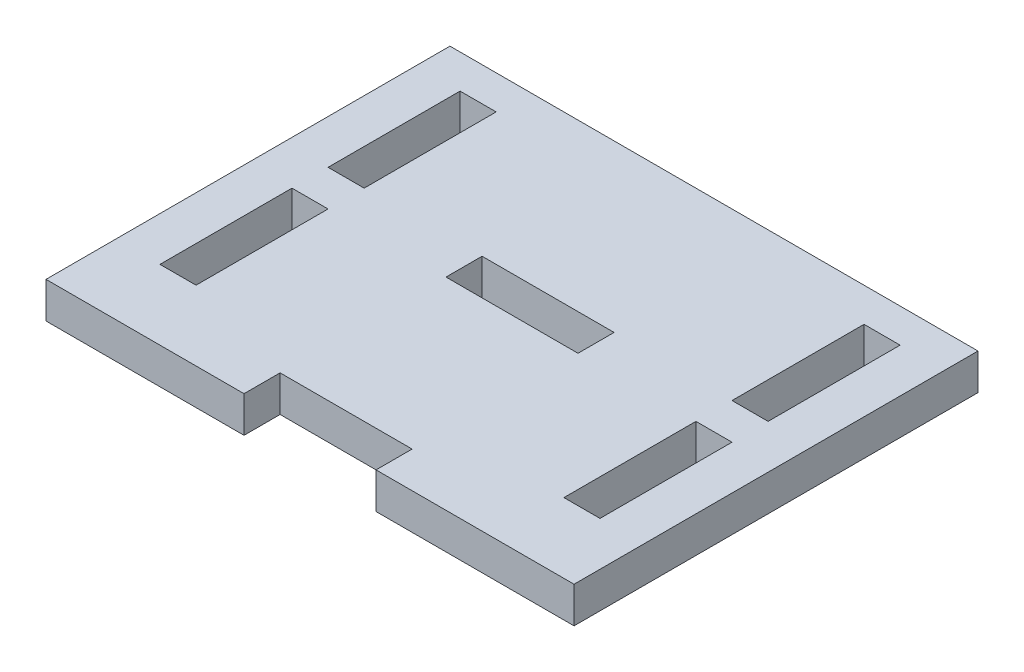
SolidWorks part; units mm, degrees
ref_plane "Front" through (0, 0, 0) normal (0, 0, 1) x (1, 0, 0)
ref_plane "Top" through (0, 0, 0) normal (0, 1, 0) x (1, 0, 0)
ref_plane "Right" through (0, 0, 0) normal (1, 0, 0) x (0, 0, -1)
sketch "Sketch1" plane through (0, 0, 0) normal (0, 1, 0) x (1, 0, 0)
  line L0 (0, 45.9) -> (0, 0)
  line L1 (0, 0) -> (60, 0) construction
  line L2 (30, 45.9) -> (30, 0) construction
  line L4 (60, 0) -> (60, 45.9)
  line L5 (5, 42.05) -> (9.1, 42.05)
  line L6 (5, 42.05) -> (5, 27.05)
  line L7 (5, 27.05) -> (9.1, 27.05)
  line L8 (9.1, 42.05) -> (9.1, 27.05)
  line L9 (60, 25) -> (0, 25) construction
  line L10 (5, 7.95) -> (9.1, 7.95)
  line L11 (5, 7.95) -> (5, 22.95)
  line L12 (5, 22.95) -> (9.1, 22.95)
  line L13 (9.1, 7.95) -> (9.1, 22.95)
  line L14 (55, 42.05) -> (50.9, 42.05)
  line L15 (55, 42.05) -> (55, 27.05)
  line L16 (50.9, 42.05) -> (50.9, 27.05)
  line L17 (55, 27.05) -> (50.9, 27.05)
  line L18 (55, 7.95) -> (55, 22.95)
  line L19 (55, 7.95) -> (50.9, 7.95)
  line L20 (50.9, 7.95) -> (50.9, 22.95)
  line L21 (55, 22.95) -> (50.9, 22.95)
  line L22 (22.5, 0) -> (0, 0)
  line L23 (22.5, 22.95) -> (37.5, 22.95)
  line L24 (22.5, 22.95) -> (22.5, 27.05)
  line L25 (22.5, 27.05) -> (37.5, 27.05)
  line L26 (37.5, 22.95) -> (37.5, 27.05)
  line L27 (22.5, 22.95) -> (37.5, 27.05) construction
  line L28 (22.5, 27.05) -> (37.5, 22.95) construction
  line L29 (37.5, 0) -> (60, 0)
  line L30 (22.5, 0) -> (22.5, 4.1)
  line L31 (22.5, 4.1) -> (37.5, 4.1)
  line L32 (37.5, 0) -> (37.5, 4.1)
  line L33 (0, 45.9) -> (60, 45.9)
  point P25 (30, 25)
  dimension "D2" = 60
  dimension "D3" = 3.85
  dimension "D4" = 15
  dimension "D5" = 4.1
  dimension "D6" = 5
  dimension "D7" = 15
  dimension "D8" = 4.1
  dimension "D9" = 15
  dimension "D10" = 4.1
  dimension "D11" = 45.9
  dimension "D12" = 20.9
extrude "Boss-Extrude1" add sketch "Sketch1" along normal blind 4.1
